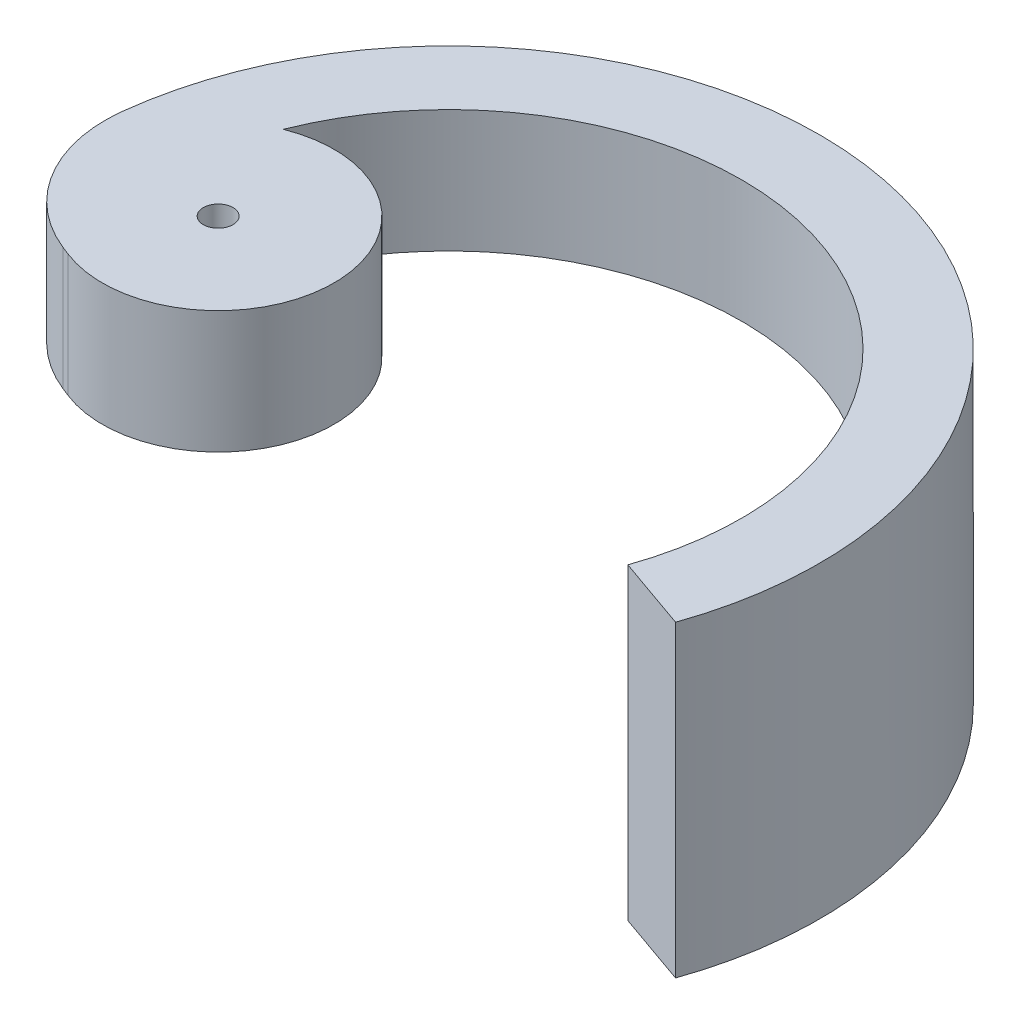
SolidWorks part; units mm, degrees
ref_plane "Front Plane" through (0, 0, 0) normal (0, 0, 1) x (1, 0, 0)
ref_plane "Top Plane" through (0, 0, 0) normal (0, 1, 0) x (1, 0, 0)
ref_plane "Right Plane" through (0, 0, 0) normal (1, 0, 0) x (0, 0, -1)
sketch "Sketch4" plane through (0, 0, 0) normal (0, 1, 0) x (1, 0, 0)
  line L0 (-18.663, -7.3713) -> (-24.9238, -4.8955)
  line L1 (18.9326, -6.6484) -> (23.9653, -8.4157)
  arc A0 (23.9653, -8.4157) -> (-24.9238, -4.8955) centre (0, 0) ccw
  arc A1 (18.9326, -6.6484) -> (-18.663, 7.3713) centre (0, 0) ccw
  circle A2 centre (-15.748, 0) radius 1.016
  arc A3 (-18.663, -7.3713) -> (-18.663, 7.3713) centre (-15.748, 0) ccw
extrude "Boss-Extrude3" add sketch "Sketch4" along normal blind 8.382
sketch "Sketch5" plane through (0, 0, 0) normal (0, -1, 0) x (1, 0, 0)
  line L0 (18.9326, 6.6484) -> (23.9653, 8.4157)
  line L1 (13.2981, -15.0268) -> (16.833, -19.0213)
  arc A0 (16.833, -19.0213) -> (23.9653, 8.4157) centre (0, 0) ccw
  arc A1 (13.2981, -15.0268) -> (18.9326, 6.6484) centre (0, 0) ccw
extrude "Boss-Extrude4" add sketch "Sketch5" along normal blind 12.7
fillet "Fillet4" radius 9.652 1 edges at (-24.9238, 4.191, 4.8955)
